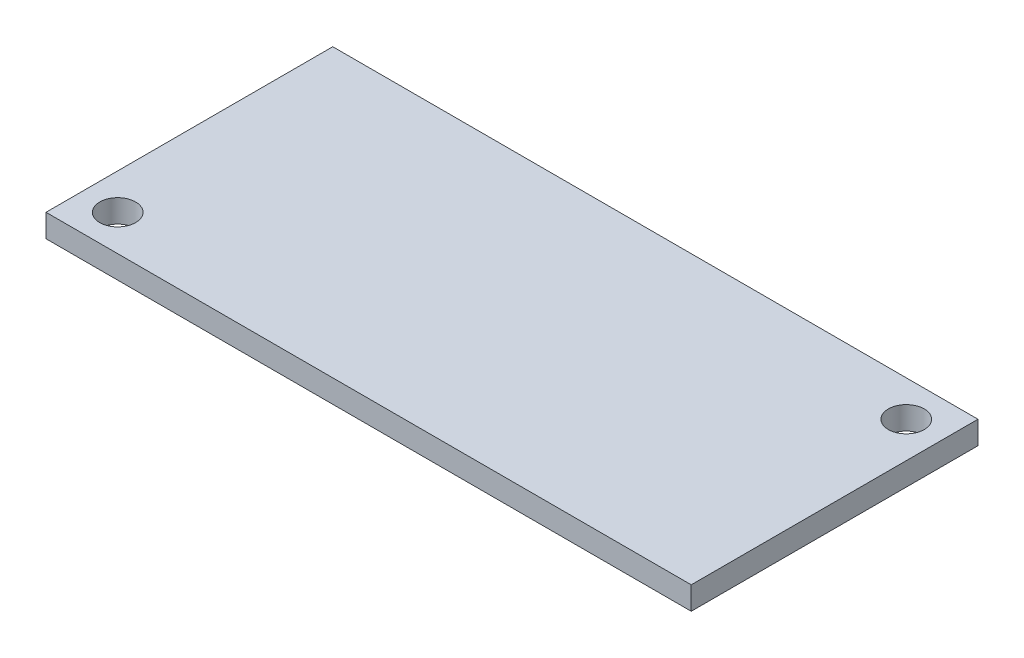
SolidWorks part; units mm, degrees
material "ABS"
ref_plane "Front Plane" through (0, 0, 0) normal (0, 0, 1) x (1, 0, 0)
ref_plane "Top Plane" through (0, 0, 0) normal (0, 1, 0) x (1, 0, 0)
ref_plane "Right Plane" through (0, 0, 0) normal (1, 0, 0) x (0, 0, -1)
sketch "Sketch1" plane through (0, 0, 0) normal (0, 1, 0) x (1, 0, 0)
  line L1 (-22.5, -10) -> (22.5, -10)
  line L2 (-22.5, -10) -> (-22.5, 10)
  line L3 (-22.5, 10) -> (22.5, 10)
  line L4 (22.5, -10) -> (22.5, 10)
  line L5 (-22.5, -10) -> (22.5, 10) construction
  line L6 (-22.5, 10) -> (22.5, -10) construction
  point P0 (0, 0)
  dimension "D1" = 45
  dimension "D2" = 20
extrude "Boss-Extrude1" add sketch "Sketch1" along normal blind 1.6
sketch "Sketch8" plane through (0, 1.6, 0) normal (0, 1, 0) x (1, 0, 0)
  line L0 (-22.5, 10) -> (-22.5, -10) construction
  line L1 (22.5, 10) -> (-22.5, 10) construction
  line L2 (-22.5, -10) -> (22.5, -10) construction
  line L3 (0, -10) -> (0, 10.0491) construction
  line L4 (-22.5, 0) -> (22.518, 0) construction
  line L5 (22.5, -10) -> (22.5, 10) construction
  circle A0 centre (-20, -7.5) radius 1.25
  circle A1 centre (20, 7.5) radius 1.25
  dimension "D1" = 2.5
  dimension "D2" = 2.5
  dimension "D3" = 2.5
  dimension "D4" = 2.5
  dimension "D5" = 2.5
extrude "Cut-Extrude3" cut sketch "Sketch8" against normal through all
